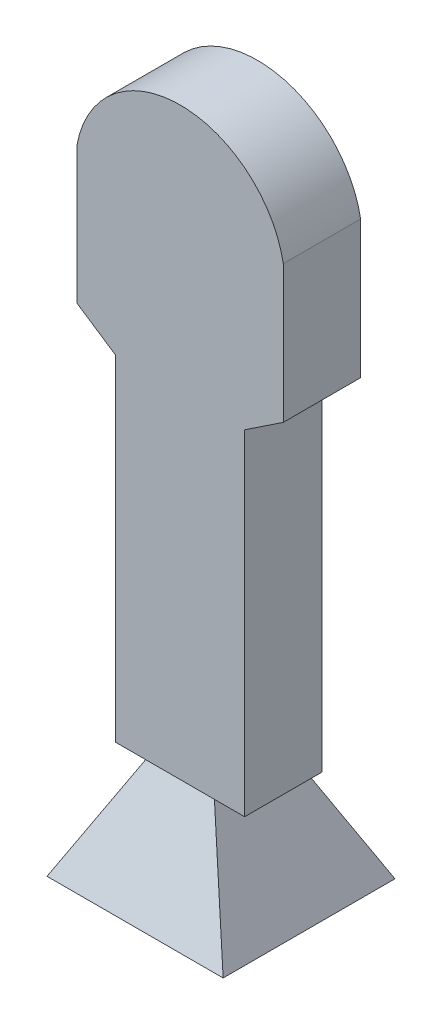
SolidWorks part; units mm, degrees
ref_plane "Plano frontal" through (0, 0, 0) normal (0, 0, 1) x (1, 0, 0)
ref_plane "Plano superior" through (0, 0, 0) normal (0, 1, 0) x (1, 0, 0)
ref_plane "Plano direito" through (0, 0, 0) normal (1, 0, 0) x (0, 0, -1)
sketch "Esboço1" plane through (0, 0, 0) normal (0, 0, 1) x (1, 0, 0)
  line L0 (0, 10.9909) -> (0, 18) construction
  line L2 (-12, 1) -> (-12, -15)
  line L4 (12, 1) -> (12, -15)
  line L8 (-7.5, -18) -> (-7.5, -57)
  line L9 (-7.5, -57) -> (-4, -57)
  line L10 (7.5, -57) -> (7.5, -18)
  line L11 (-10, -69) -> (10, -69)
  line L12 (12, -15) -> (7.5, -18)
  line L13 (-12, -15) -> (-7.5, -18)
  line L14 (-10, -69) -> (-4, -57)
  line L15 (4, -57) -> (10, -69)
  line L16 (4, -57) -> (7.5, -57)
  arc A0 (-12, 1) -> (12, 1) centre (0, -1.2111) cw
  point P0 (0, 0)
  point P11 (0, -57)
  point P12 (0, -8)
  point P22 (0, -69)
extrude "Ressalto-extrusão2" add sketch "Esboço1" along normal blind 4.5 and the other way blind 4.5
sketch "Esboço2" plane through (0, 0, 0) normal (0, 0, 1) x (1, 0, 0)
  line L1 (-8.5, -68) -> (8.5, -68)
  line L2 (-6.5, -56.1094) -> (-3, -56.1094)
  line L3 (3, -56.1094) -> (6.5, -56.1094)
  line L4 (-6.5, -56.1094) -> (-6.5, -17.1351)
  line L5 (6.5, -56.1094) -> (6.5, -17.1351)
  line L8 (-11, 0) -> (-11, -14)
  line L9 (11, 0) -> (11, -14)
  line L11 (8.5, -68) -> (3, -57.0637)
  line L12 (-3, -57.0637) -> (-8.5, -68)
  line L13 (3, -57.0637) -> (3, -56.1094)
  line L14 (-3, -57.0637) -> (-3, -56.1094)
  line L15 (11, -14) -> (6.5, -17.1351)
  line L16 (-11, -14) -> (-6.5, -17.1351)
  arc A1 (-11, 0) -> (11, 0) centre (0, -1.0764) cw
  point P4 (0, 0)
  point P9 (0, -56.1094)
  point P19 (0, -68)
  point P23 (0, -57.0637)
extrude "Corte-extrusão1" cut sketch "Esboço2" against normal blind 3.5 and the other way blind 3.5
sketch "Esboço4" plane through (0, 0, 0) normal (1, 0, 0) x (0, 0, -1)
  line L0 (0, -69) -> (10, -69)
  line L1 (4.5, -69) -> (-4.5, -69) construction
  line L2 (0, -69) -> (-10, -69)
  line L3 (-10, -69) -> (-4.5, -57)
  line L4 (-4.5, -69) -> (-4.5, -57) construction
  line L5 (4.5, -57) -> (-4.5, -57) construction
  line L6 (-4.5, -57) -> (4.5, -57)
  line L7 (4.5, -57) -> (10, -69)
extrude "Ressalto-extrusão3" add sketch "Esboço4" along normal blind 10.5 and the other way blind 10
sketch "Esboço5" plane through (0, 0, 0) normal (0, 0, 1) x (1, 0, 0)
  line L1 (-7.5, -57) -> (7.5, -57) construction
  line L2 (-4.0159, -57) -> (-10, -69)
  line L3 (-10, -69) -> (-10, -57)
  line L4 (-10, -57) -> (-4.0159, -57)
  line L5 (3.9841, -57) -> (10.5, -69)
  line L6 (10.5, -69) -> (10.5, -57)
  line L7 (10.5, -57) -> (3.9841, -57)
  point P5 (-0.0159, -57)
extrude "Corte-extrusão2" cut sketch "Esboço5" against normal blind 18.5 and the other way blind 20
sketch "Esboço6" plane through (0, -69, 0) normal (0, -1, 0) x (-1, 0, 0)
  line L1 (1.5106, 1.6628) -> (-1.5106, 1.6628)
  line L2 (1.5106, 1.6628) -> (1.5106, -1.6628)
  line L3 (1.5106, -1.6628) -> (-1.5106, -1.6628)
  line L4 (-1.5106, 1.6628) -> (-1.5106, -1.6628)
  line L5 (1.5106, 1.6628) -> (-1.5106, -1.6628) construction
  line L6 (1.5106, -1.6628) -> (-1.5106, 1.6628) construction
  point P1 (0, 0)
extrude "Corte-extrusão3" cut sketch "Esboço6" against normal blind 12.5 and the other way blind 17
